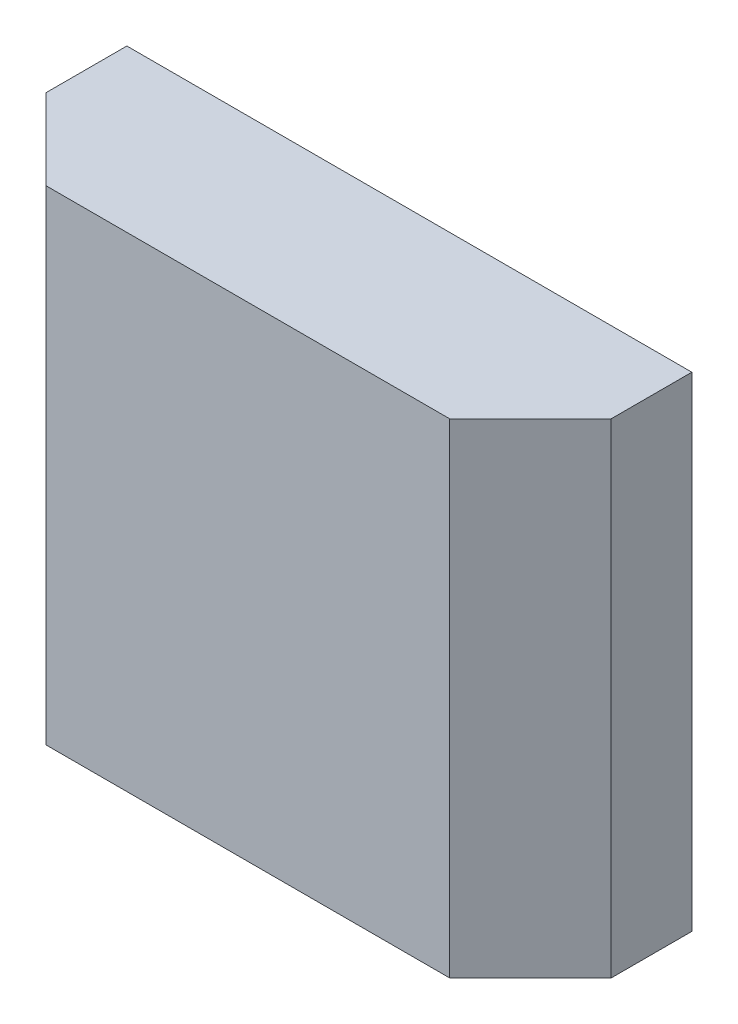
SolidWorks part; units mm, degrees
ref_plane "Front Plane" through (0, 0, 0) normal (0, 0, 1) x (1, 0, 0)
ref_plane "Top Plane" through (0, 0, 0) normal (0, 1, 0) x (1, 0, 0)
ref_plane "Right Plane" through (0, 0, 0) normal (1, 0, 0) x (0, 0, -1)
sketch "Sketch1" plane through (0, 0, 0) normal (0, 1, 0) x (1, 0, 0)
  line L0 (-3.5, 1) -> (3.5, 1)
  line L1 (3.5, 1) -> (3.5, 0)
  line L2 (3.5, 0) -> (2.5, -1)
  line L3 (2.5, -1) -> (-2.5, -1)
  line L4 (-2.5, -1) -> (-3.5, 0)
  line L5 (-3.5, 0) -> (-3.5, 1)
  line L6 (0, 1) -> (0, -1) construction
  dimension "D1" = 7
  dimension "D2" = 2
  dimension "D3" = 45
  dimension "D4" = 5
extrude "Boss-Extrude1" add sketch "Sketch1" along normal blind 6
